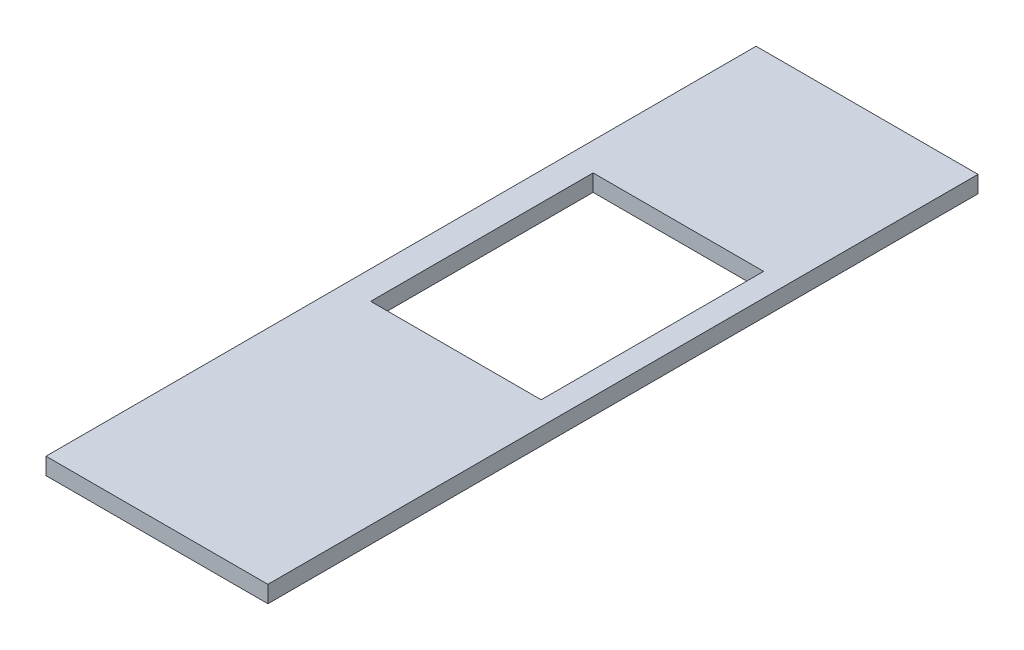
SolidWorks part; units mm, degrees
ref_plane "Спереди" through (0, 0, 0) normal (0, 0, 1) x (1, 0, 0)
ref_plane "Сверху" through (0, 0, 0) normal (0, 1, 0) x (1, 0, 0)
ref_plane "Справа" through (0, 0, 0) normal (1, 0, 0) x (0, 0, -1)
sketch "Эскиз1" plane through (0, 0, 0) normal (0, 1, 0) x (1, 0, 0)
  line L0 (0, 0) -> (0, 1600)
  line L1 (0, 1600) -> (500, 1600)
  line L2 (500, 1600) -> (500, 0)
  line L5 (500, 0) -> (0, 0)
  dimension "D1" = 500
  dimension "D2" = 1600
extrude "Бобышка-Вытянуть1" add sketch "Эскиз1" along normal blind 38
sketch "Эскиз2" plane through (0, 38, 0) normal (0, 1, 0) x (1, 0, 0)
  line L1 (63.5683, 1169.1773) -> (447.7841, 1169.1773)
  line L2 (63.5683, 1169.1773) -> (63.5683, 667.9478)
  line L3 (63.5683, 667.9478) -> (447.7841, 667.9478)
  line L4 (447.7841, 1169.1773) -> (447.7841, 667.9478)
extrude "Вырез-Вытянуть1" cut sketch "Эскиз2" against normal through all
